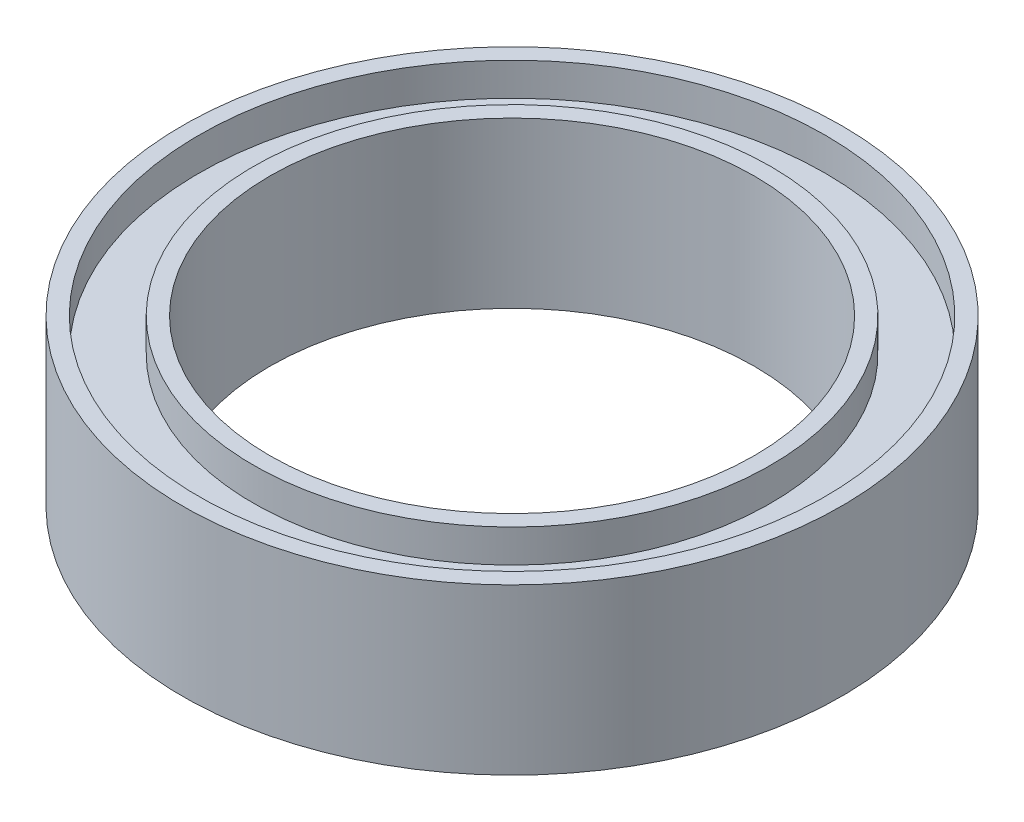
SolidWorks part; units mm, degrees
ref_plane "Front Plane" through (0, 0, 0) normal (0, 0, 1) x (1, 0, 0)
ref_plane "Top Plane" through (0, 0, 0) normal (0, 1, 0) x (1, 0, 0)
ref_plane "Right Plane" through (0, 0, 0) normal (1, 0, 0) x (0, 0, -1)
sketch "Sketch2" plane through (0, 0, 0) normal (0, 0, 1) x (1, 0, 0)
  line L0 (0, 0) -> (0, 50)
  line L1 (0, 50) -> (5, 50)
  line L2 (5, 50) -> (5, 40)
  line L3 (5, 32) -> (5, 0)
  line L4 (0, 0) -> (5, 0)
  line L5 (26.5, 50) -> (26.5, 0)
  line L6 (5, 40) -> (21.5, 40)
  line L8 (5, 32) -> (21.5, 32)
  line L11 (21.5, 32) -> (21.5, 0)
  line L12 (21.5, 0) -> (26.5, 0)
  line L15 (21.5, 40) -> (21.5, 50)
  line L16 (21.5, 50) -> (26.5, 50)
  line L17 (0, 0) -> (-73.5, 0)
  line L18 (-73.5, 0) -> (-73.5, 90.0815) construction
  dimension "D1" = 16.5
  dimension "D2" = 5
  dimension "D3" = 50
  dimension "D4" = 50
  dimension "D5" = 5
  dimension "D6" = 8
  dimension "D7" = 10
  dimension "D8" = 10
  dimension "D9" = 16.5
  dimension "D10" = 5
  dimension "D11" = 73.5
revolve "Revolve1" add sketch "Sketch2" angle 360 about L18
